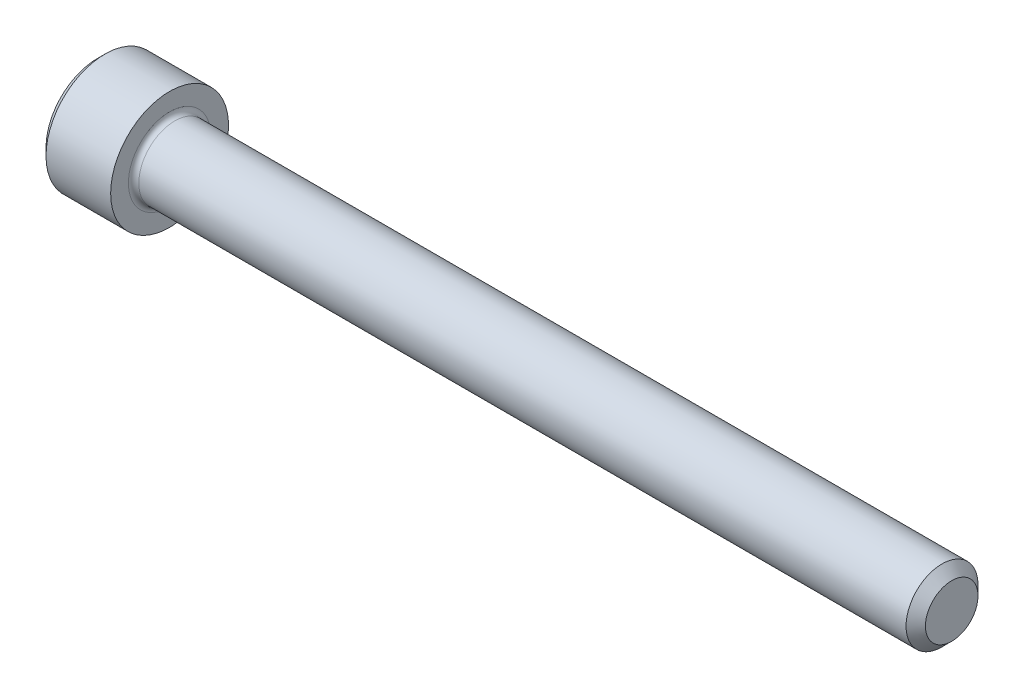
SolidWorks part; units mm, degrees
material "Alloy Steel"
ref_plane "Plane1" through (0, 0, 0) normal (0, 0, 1) x (1, 0, 0)
ref_plane "Plane2" through (0, 0, 0) normal (0, 1, 0) x (1, 0, 0)
ref_plane "Plane3" through (0, 0, 0) normal (1, 0, 0) x (0, 0, -1)
sketch "BodySke" plane through (0, 0, 0) normal (0, 0, 1) x (1, 0, 0)
  line L0 (0, 0) -> (0, 2.5146)
  line L1 (0.3556, 2.8702) -> (3.5052, 2.8702)
  line L2 (3.5052, 2.8702) -> (3.5052, 1.7526)
  line L3 (3.5052, 1.7526) -> (41.1328, 1.7526)
  line L4 (41.6052, 1.2802) -> (41.6052, 0)
  line L5 (41.6052, 0) -> (0, 0)
  line L6 (-31.75, 0) -> (127, 0) construction
  line L7 (0, 2.5146) -> (0.3556, 2.8702)
  line L8 (41.6052, 1.2802) -> (41.1328, 1.7526)
  line L9 (0, -2.5146) -> (0.3556, -2.8702) construction
  line L10 (41.6052, -1.2802) -> (41.1328, -1.7526) construction
  line L11 (4.2977, 9.525) -> (4.2977, 3.175) construction
  line L12 (16.2052, 9.525) -> (16.2052, 3.175) construction
  line L13 (3.5052, 9.525) -> (3.5052, 3.175) construction
  dimension "Diameter" = 3.5052
  dimension "Head_ht" = 3.5052
  dimension "Length" = 38.1
  dimension "Body_ch_ang" = 45
  dimension "Head_dia" = 5.7404
  dimension "Head_ch_ang" = 45
  dimension "Head_side_ht" = 3.1496
  dimension "Minor_dia" = 2.5603
  dimension "Advance" = 0.7925
  dimension "Thread_nom" = 25.4
  dimension "Thread_length" = 38.1
revolve "Base-Revolve" add sketch "BodySke"
cosmetic thread "ThreadCosmetic"
fillet "Fillet1" radius 0.254 1 edges at (3.5052, 0, 1.7526)
sketch "Sketch2" plane through (0, 0, 0) normal (0, 0, 1) x (1, 0, 0)
  line L0 (0, 1.3843) -> (1.6256, 1.3843)
  line L1 (1.6256, 1.3843) -> (2.4248, 0)
  line L2 (-31.75, 0) -> (127, 0) construction
  line L3 (2.4248, 0) -> (0, 0)
  line L4 (0, 0) -> (0, 1.3843)
  line L5 (0, 2.5146) -> (0, -2.5146) construction
  line L6 (0, 0) -> (47.625, 0) construction
  line L7 (3.5052, -2.8702) -> (3.5052, 2.8702) construction
  dimension "D1" = 1.3843
  dimension "D2" = 60
  dimension "Wall_thickness" = 1.8796
revolve "Hex-PreBroach" cut sketch "Sketch2" angle 360 about L6
sketch "Sketch3" plane through (0, 0, 0) normal (-1, 0, 0) x (0, 0.5, 0.866)
  line L0 (0.7992, 1.3843) -> (-0.7992, 1.3843)
  line L1 (-0.7992, 1.3843) -> (-1.5985, 0)
  line L2 (0.7992, 1.3843) -> (1.5985, 0)
  line L3 (0.7992, -1.3843) -> (1.5985, 0)
  line L4 (0.7992, -1.3843) -> (-0.7992, -1.3843)
  line L5 (-0.7992, -1.3843) -> (-1.5985, 0)
  dimension "D1" = 1.3843
  dimension "D2" = 1.3843
  dimension "Hex_size" = 2.7686
extrude "Hex" cut sketch "Sketch3" against normal blind 1.6256
sketch "Sketch4" plane through (0, 0, 0) normal (-1, 0, 0) x (0, 0, 1)
  line L0 (0, 0) -> (1.7399, 0)
  line L1 (0, 0) -> (6.1484, 3.5498) construction
  line L2 (0, 0) -> (0.8699, 1.5068)
  line L3 (1.4457, 0.3947) -> (1.6607, 0.5189)
  line L4 (1.0647, 1.0546) -> (1.2797, 1.1788)
  arc A0 (1.4457, 0.3947) -> (1.0647, 1.0546) centre (0, 0) ccw
  arc A1 (1.7399, 0) -> (1.6607, 0.5189) centre (0, 0) ccw
  arc A2 (0.8699, 1.5068) -> (1.2797, 1.1788) centre (0, 0) cw
  dimension "D1" = 30
  dimension "Spline_n_dim" = 2.9972
  dimension "Spline_m_dim" = 3.4798
  dimension "D2" = 60
  dimension "D3" = 0.381
  dimension "Spline_p_dim" = 0.762
extrude "Spline" [suppressed] cut sketch "Sketch4" against normal blind 1.6256
pattern_circular "CirPattern1" [suppressed] count 6 every 60
sketch "Sketch5" plane through (0, 0, 0) normal (0, 0, 1) x (1, 0, 0)
  line L0 (-31.75, 0) -> (127, 0) construction
  line L2 (0, 2.5146) -> (0, -2.5146) construction
  circle A0 centre (1.27, 0) radius 0.4445
  dimension "Drilled_hole_dia" = 0.889
  dimension "Drilled_hole_loc" = 1.27
extrude "Hole" [suppressed] cut sketch "Sketch5" against normal through all and the other way through all
pattern_circular "Drilled-4" [suppressed] count 2 every 60
pattern_circular "Drilled-6" [suppressed] count 3 every 60
sketch "ThdSchSke" plane through (0, 0, 0) normal (0, 0, 1) x (1, 0, 0)
  line L0 (16.2052, -1.2802) -> (15.8744, -1.7526)
  line L1 (16.2052, -1.2802) -> (16.536, -1.7526)
  line L2 (16.536, -1.7526) -> (16.536, -2.1908)
  line L3 (-3.175, 0) -> (5.1513, 0) construction
  line L5 (16.536, -2.1908) -> (15.8744, -2.1908)
  line L6 (15.8744, -2.1908) -> (15.8744, -1.7526)
  line L7 (0, 2.5146) -> (0, -2.5146) construction
  dimension "Thread_minor" = 2.5603
  dimension "Diameter" = 3.5052
  dimension "Start" = 16.2052
  dimension "SideAngle" = 55
  dimension "VeeAngle" = 70
  dimension "Overcut" = 4.3815
revolve "ThreadSchematic" [suppressed] cut sketch "ThdSchSke" angle 360 about L3
pattern_linear "ThdSchPat" [suppressed]
equation "\"D2@Sketch3\" = \"Hex_size@Sketch3\" / 2"
equation "\"D1@Sketch3\" = \"Hex_size@Sketch3\" / 2"
equation "\"D1@Sketch2\" = \"Hex_size@Sketch3\" / 2"
equation "\"D3@Sketch4\" = \"Spline_p_dim@Sketch4\" / 2"
equation "\"Thread_minor@ThreadCosmetic\"  =  \"Minor_dia@BodySke\""
equation "\"D2@CirPattern1\" = 360 / \"Num_teeth@CirPattern1\""
equation "\"Wall_thickness@Sketch2\" = \"Head_ht@BodySke\" - \"Key_eng@Hex\""
equation "\"Thread_length@ThreadCosmetic\" = ((sgn( (\"Length@BodySke\" - \"Advance@BodySke\" ) - \"Thread_nom@BodySke\" )-1)*( (\"Length@BodySke\" - \"Advance@BodySke\" ) - \"Thread_nom@BodySke\" ))/-2+ \"Thread_nom@BodySke\""
equation "\"Thread_minor@ThdSchSke\" = \"Minor_dia@BodySke\""
equation "\"Diameter@ThdSchSke\" = \"Diameter@BodySke\""
equation "\"Overcut@ThdSchSke\" = \"Diameter@BodySke\" * 1.25"
equation "\"Start@ThdSchSke\" = \"Head_ht@BodySke\" + \"Length@BodySke\" - \"Thread_length@ThreadCosmetic\"  '---Non-countersunk---"
equation "\"Num_threads@ThdSchPat\" = int( \"Thread_length@ThreadCosmetic\" / \"Advance@BodySke\" + 0.999 )  + 1"
equation "\"Advance@ThdSchPat\" = \"Thread_length@ThreadCosmetic\" /  (\"Num_threads@ThdSchPat\" - 1) 'relax it"
equation "\"Num_threads@ThdSchPat\" = \"Num_threads@ThdSchPat\" - sgn( \"Num_threads@ThdSchPat\" - 1) '---chamfered tips only---"
